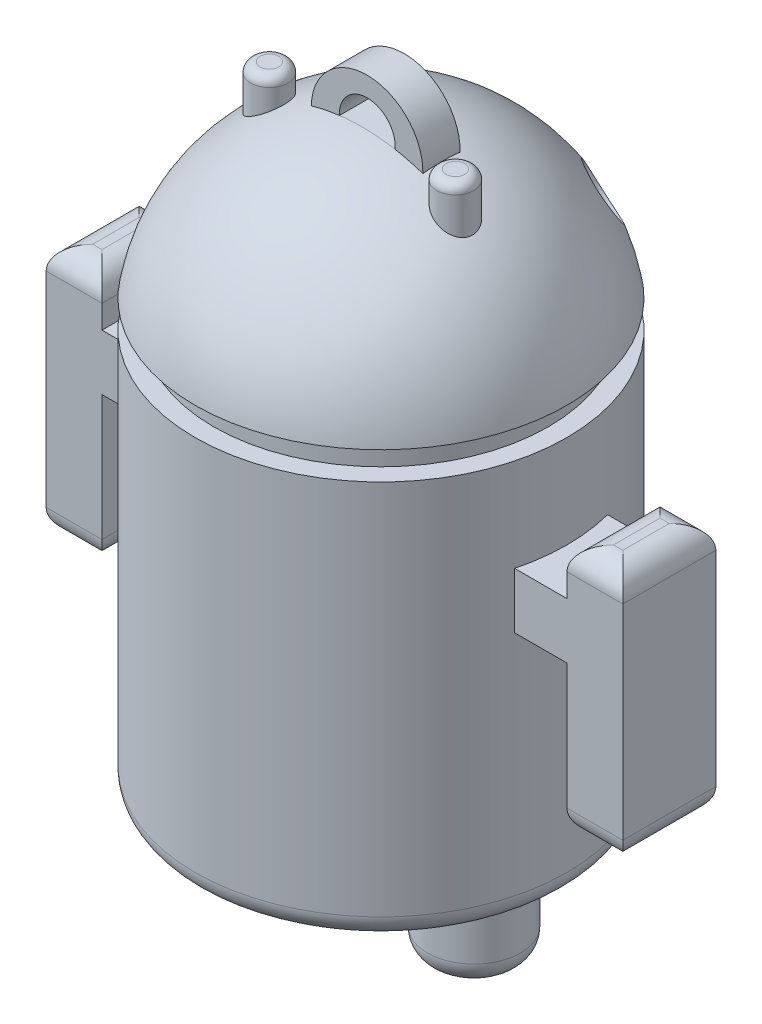
SolidWorks part; units mm, degrees
ref_plane "Alzado" through (0, 0, 0) normal (0, 0, 1) x (1, 0, 0)
ref_plane "Planta" through (0, 0, 0) normal (0, 1, 0) x (1, 0, 0)
ref_plane "Vista lateral" through (0, 0, 0) normal (1, 0, 0) x (0, 0, -1)
sketch "Croquis1" plane through (0, 0, 0) normal (0, 0, 1) x (1, 0, 0)
  line L8 (0, 63) -> (0, 0)
  line L9 (20, 43) -> (20, 0)
  line L10 (20, 0) -> (0, 0)
  line L11 (20, 43) -> (18, 43)
  line L12 (18, 43) -> (18, 46)
  line L13 (18, 46) -> (20, 46)
  arc A1 (0, 63) -> (20, 43) centre (0, 43) ccw construction
  arc A2 (0, 63) -> (20, 46) centre (0, 42.7353) cw
  point P9 (0, 0)
  dimension "D1" = 63
  dimension "D6" = 20
  dimension "D2" = 20
  dimension "D3" = 43
  dimension "D4" = 2
  dimension "D5" = 3
  dimension "D7" = 2
revolve "Revolución1" add sketch "Croquis1" angle 360 about L8
sketch "Croquis2" plane through (0, 0, 0) normal (0, 0, 1) x (1, 0, 0)
  line L0 (0, 81.4364) -> (0, -16.608) construction
  line L1 (-20, 46) -> (20, 46) construction
  circle A0 centre (-8, 52) radius 3
  circle A1 centre (8, 52) radius 3
  dimension "D1" = 8
  dimension "D3" = 6
  dimension "D2" = 6
extrude "Cortar-Extruir1" cut sketch "Croquis2" against normal through all
sketch "Croquis9" plane through (0, 0, 0) normal (0, 1, 0) x (1, 0, 0)
  line L0 (1.7714, 0) -> (-24.3358, 0) construction
  circle A0 centre (-10, -2) radius 2
  circle A1 centre (0, 0) radius 20 construction
  dimension "D1" = 4
  dimension "D2" = 10
  dimension "D3" = 2
extrude "Saliente-Extruir4" add sketch "Croquis9" along normal blind 64
sketch "Croquis12" plane through (0, 0, 0) normal (0, 1, 0) x (1, 0, 0)
  line L0 (22.7254, 0) -> (-24.9442, 0) construction
  line L1 (0, -10.3399) -> (0, 13.115) construction
  circle A0 centre (-10, 0) radius 5
  dimension "D1" = 10
  dimension "D2" = 0
  dimension "D3" = 10
extrude "Saliente-Extruir7" add sketch "Croquis12" against normal blind 10 contours A0
sketch "Croquis17" plane through (0, 0, 0) normal (0, 0, 1) x (1, 0, 0)
  line L0 (28.6875, 30) -> (-34.6279, 30) construction
  line L2 (-5, 27) -> (-25, 27)
  line L4 (-25, 33) -> (-5, 33)
  line L6 (-25, 33) -> (-25, 38)
  line L7 (-25, 38) -> (-31, 38)
  line L8 (-31, 38) -> (-31, 11)
  line L9 (-31, 11) -> (-25, 11)
  line L10 (-25, 11) -> (-25, 27)
  line L11 (-25, 33) -> (-25, 38)
  line L12 (-5, 27) -> (-5, 33)
  line L15 (-20, 43) -> (-20, 0) construction
  dimension "D1" = 6
  dimension "D2" = 27
  dimension "D3" = 16
  dimension "D4" = 20
  dimension "D5" = 6
  dimension "D6" = 20
  dimension "D7" = 5
  dimension "D8" = 5
  dimension "D9" = 30
extrude "Saliente-Extruir8" add sketch "Croquis17" along normal mid plane 10 contours L0 L12 L4 L6 L7 L8 | L12 L0 L8 L9 L10 L2
mirror "Simetría4" about plane through (0, 0, 0) normal (1, 0, 0) of "Saliente-Extruir7", "Saliente-Extruir8", "Saliente-Extruir4"
sketch "Croquis18" plane through (0, 0, 0) normal (0, 0, 1) x (1, 0, 0)
  line L0 (20, 43) -> (-20, 43) construction
  line L1 (-8, 61.2463) -> (-8, 64) construction
  line L2 (25.3604, 62) -> (-30.173, 62) construction
  circle A0 centre (0.5, 62) radius 6
  circle A1 centre (0.5, 62) radius 3.5 construction
  dimension "D1" = 19
  dimension "D2" = 12
  dimension "D4" = 62
  dimension "D5" = 2.5
  dimension "D3" = 8.5
extrude "Saliente-Extruir10" add sketch "Croquis18" along normal mid plane 4
sketch "Croquis20" plane through (0, 0, -2) normal (0, 0, -1) x (-1, 0, 0)
  circle A0 centre (-0.5232, 62.8943) radius 3 construction
  arc A1 (5.4984, 62.137) -> (-6.4975, 61.8256) centre (0, 42.7353) ccw construction
  arc A2 (-3.5081, 62.5936) -> (2.4733, 62.7488) centre (0, 42.7353) cw
  arc A3 (-3.5081, 62.5936) -> (2.4733, 62.7488) centre (-0.5232, 62.8943) cw
  arc A4 (5.4984, 62.137) -> (-6.4975, 61.8256) centre (-0.5, 62) ccw construction
  dimension "D1" = 3
  dimension "D2" = 0.8946
  dimension "D3" = 42.7353
extrude "Cortar-Extruir7" cut sketch "Croquis20" against normal blind 4
fillet "Redondeo7" radius 1 2 edges at (-10, 64, 4) (10, 64, 4)
fillet "Redondeo8" radius 2.5 2 edges at (-10, -10, 5) (10, -10, 5)
fillet "Redondeo9" radius 2.5 8 edges at (-31, 11, 0) (-28, 11, 5) (-25, 11, 0) (-28, 11, -5) (25, 11, 0) (28, 11, 5) (31, 11, 0) (28, 11, -5)
fillet "Redondeo10" radius 2.5 8 edges at (-25, 38, 0) (-28, 38, 5) (-31, 38, 0) (-28, 38, -5) (31, 38, 0) (28, 38, 5) (25, 38, 0) (28, 38, -5)
fillet "Redondeo13" radius 2.5 1 edges at (0, 0, 20)
